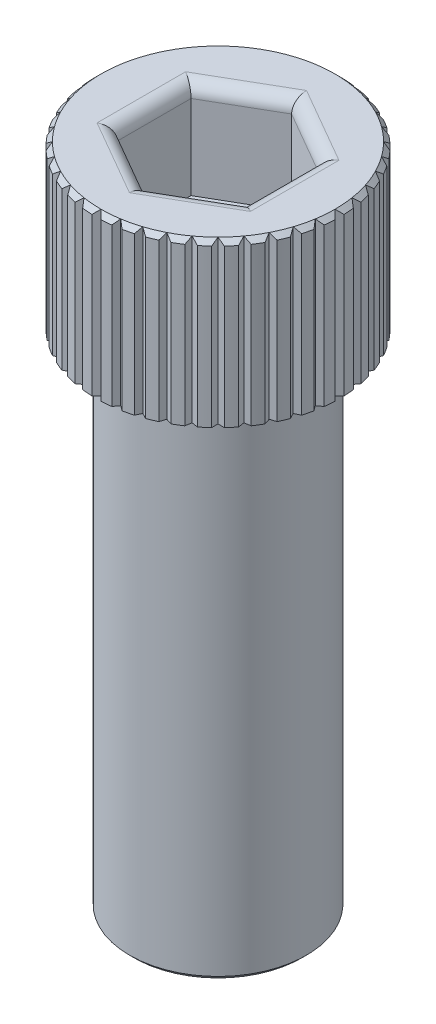
SolidWorks part; units mm, degrees
material "1060 Alloy"
ref_plane "Front Plane" through (0, 0, 0) normal (0, 0, 1) x (1, 0, 0)
ref_plane "Top Plane" through (0, 0, 0) normal (0, 1, 0) x (1, 0, 0)
ref_plane "Right Plane" through (0, 0, 0) normal (1, 0, 0) x (0, 0, -1)
sketch "Sketch1" plane through (0, 0, 0) normal (0, 0, 1) x (1, 0, 0)
  line L0 (0, 0) -> (0, 26.1112)
  line L1 (0, 26.1112) -> (4.5956, 26.1112)
  line L2 (4.7752, 25.9316) -> (4.7752, 19.7612)
  line L3 (4.7752, 19.7612) -> (3.4671, 19.7612)
  line L4 (3.4671, 19.7612) -> (3.4671, 0.1796)
  line L5 (3.2875, 0) -> (0, 0)
  line L6 (3.2875, 0) -> (3.4671, 0.1796)
  line L7 (4.5956, 26.1112) -> (4.7752, 25.9316)
  dimension "D1" = 6.35
  dimension "D2" = 3.4671
  dimension "D3" = 45
  dimension "D4" = 0.254
  dimension "D5" = 26.1112
  dimension "D6" = 4.7752
  dimension "D7" = 45
  dimension "D8" = 0.254
revolve "Revolve1" add sketch "Sketch1" angle 360 about L0
sketch "Sketch2" plane through (0, 26.1112, 0) normal (0, 1, 0) x (1, 0, 0)
  line L1 (0, -2.8893) -> (2.5022, -1.4446)
  line L2 (2.5022, -1.4446) -> (2.5022, 1.4446)
  line L3 (2.5022, 1.4446) -> (0, 2.8893)
  line L4 (0, 2.8893) -> (-2.5022, 1.4446)
  line L5 (-2.5022, 1.4446) -> (-2.5022, -1.4446)
  line L6 (-2.5022, -1.4446) -> (0, -2.8893)
  circle A0 centre (0, 0) radius 2.5022 construction
  dimension "D1" = 5.7785
extrude "Cut-Extrude1" cut sketch "Sketch2" against normal blind 3.81
fillet "Fillet1" radius 0.508 6 edges at (1.2511, 26.1112, -2.1669) (2.5022, 26.1112, 0) (1.2511, 26.1112, 2.1669) (-1.2511, 26.1112, 2.1669) (-2.5022, 26.1112, 0) (-1.2511, 26.1112, -2.1669)
sketch "Sketch3" plane through (0, 26.1112, 0) normal (0, 1, 0) x (1, 0, 0)
  line L0 (0, 0) -> (0, 6.1488) construction
  line L1 (-0.635, 5.2306) -> (0, 4.5956)
  line L2 (0, 4.5956) -> (0.635, 5.2306)
  line L3 (-0.635, 5.2306) -> (0.635, 5.2306)
  circle A0 centre (0, 0) radius 4.5956 construction
  point P9 (0, 5.2306)
  dimension "D1" = 90
  dimension "D2" = 1.27
extrude "Cut-Extrude2" cut sketch "Sketch3" against normal blind 6.604
pattern_circular "CirPattern1" count 40 over 360 about axis through (0, 0, 0) along (0, 1, 0) of "Cut-Extrude2"
